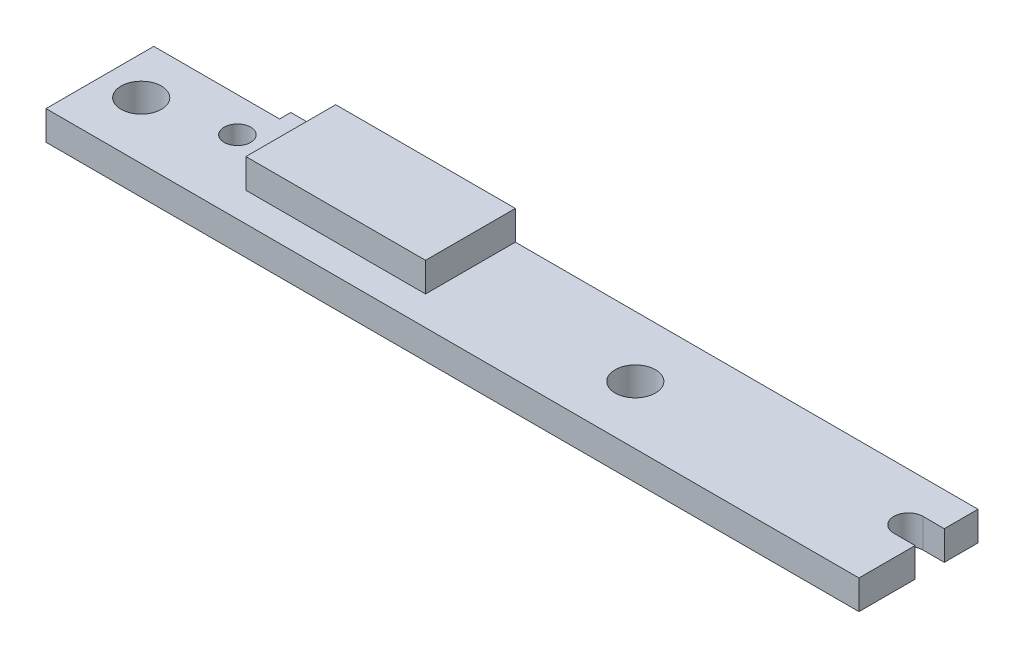
SolidWorks part; units mm, degrees
ref_plane "Front Plane" through (0, 0, 0) normal (0, 0, 1) x (1, 0, 0)
ref_plane "Top Plane" through (0, 0, 0) normal (0, 1, 0) x (1, 0, 0)
ref_plane "Right Plane" through (0, 0, 0) normal (1, 0, 0) x (0, 0, -1)
sketch "Sketch1" plane through (0, 0, 0) normal (0, 1, 0) x (1, 0, 0)
  line L0 (51.1899, 4.0005) -> (44.7675, 4.0005) construction
  line L1 (0, 0) -> (45.974, 0)
  line L2 (0, 0) -> (0, 6.731)
  line L3 (0, 6.731) -> (45.974, 6.731)
  line L4 (45.974, 0) -> (45.974, 6.731)
  line L5 (0, 6.731) -> (7.112, 6.731)
  line L6 (0, 6.731) -> (0, 6.096)
  line L7 (0, 6.096) -> (7.112, 6.096)
  line L8 (7.112, 6.731) -> (7.112, 6.096)
  line L9 (51.1899, 3.175) -> (44.7675, 3.175)
  line L10 (51.1899, 4.826) -> (44.7675, 4.826)
  line L12 (9.652, 6.731) -> (19.812, 6.731)
  line L13 (9.652, 6.731) -> (9.652, 1.651)
  line L14 (9.652, 1.651) -> (19.812, 1.651)
  line L15 (19.812, 6.731) -> (19.812, 1.651)
  arc A0 (51.1899, 3.175) -> (51.1899, 4.826) centre (51.1899, 4.0005) ccw
  arc A1 (44.7675, 4.826) -> (44.7675, 3.175) centre (44.7675, 4.0005) ccw
  circle A2 centre (2.159, 3.2258) radius 1.143
  circle A3 centre (6.6936, 4.1282) radius 0.75
  circle A4 centre (30.0228, 3.302) radius 1.143
  point P10 (47.9787, 4.0005)
  point P25 (30.0228, 4.445)
  point P26 (43.942, 4.0005)
  point P27 (31.1658, 3.302)
  point P28 (1.016, 3.2258)
  point P29 (2.159, 2.0828)
  point P30 (5.9436, 4.1282)
  point P31 (6.6936, 3.3782)
  point P32 (2.159, 2.0828)
  dimension "D3" = 0.635
  dimension "D5" = 2.286
  dimension "D6" = 1.5
  dimension "D7" = 2.286
  dimension "D1" = 45.974
  dimension "D2" = 6.731
  dimension "D4" = 7.112
  dimension "D8" = 5.08
  dimension "D9" = 19.812
  dimension "D10" = 9.652
  dimension "D11" = 1.651
  dimension "D12" = 2.032
  dimension "D13" = 1.905
  dimension "D14" = 2.286
  dimension "D15" = 14.8082
  dimension "D16" = 1.016
  dimension "D17" = 2.0828
  dimension "D18" = 5.9436
  dimension "D19" = 3.3782
extrude "Boss-Extrude1" add sketch "Sketch1" along normal blind 1.651 contours A1 L10 L4 L3 L15 L14 L13 L8 L7 L2 L1 L9 A4 A3 A2
sketch "Sketch2" plane through (0, 1.651, 0) normal (0, 1, 0) x (1, 0, 0)
  line L1 (9.652, 6.731) -> (19.812, 6.731)
  line L2 (9.652, 6.731) -> (9.652, 1.651)
  line L3 (9.652, 1.651) -> (19.812, 1.651)
  line L4 (19.812, 6.731) -> (19.812, 1.651)
extrude "Boss-Extrude2" add sketch "Sketch2" along normal blind 1.651 and the other way up to surface (1.651 mm away) other way up to face at (30.0228, 0, -2.159)
